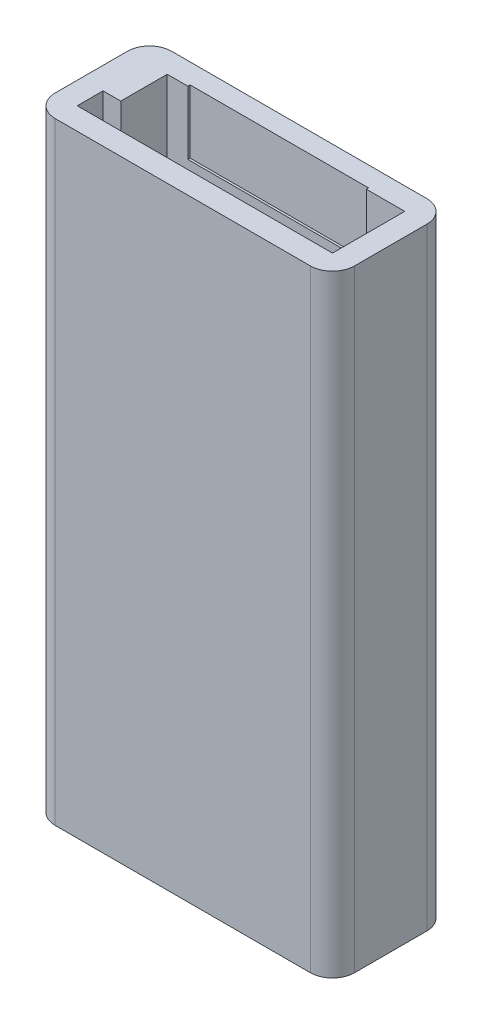
SolidWorks part; units mm, degrees
ref_plane "Front Plane" through (0, 0, 0) normal (0, 0, 1) x (1, 0, 0)
ref_plane "Top Plane" through (0, 0, 0) normal (0, 1, 0) x (1, 0, 0)
ref_plane "Right Plane" through (0, 0, 0) normal (1, 0, 0) x (0, 0, -1)
sketch "Sketch1" plane through (0, 0, 0) normal (0, 1, 0) x (1, 0, 0)
  line L0 (10.15, -3.95) -> (10.15, 3.95)
  line L1 (8.65, -2.45) -> (-8.65, -2.45)
  line L2 (8.65, -2.45) -> (8.65, 2.45)
  line L3 (8.65, 2.45) -> (-8.65, 2.45)
  line L4 (-8.65, -2.45) -> (-8.65, 2.45)
  line L5 (8.65, -2.45) -> (-8.65, 2.45) construction
  line L6 (8.65, 2.45) -> (-8.65, -2.45) construction
  line L7 (10.15, 3.95) -> (-10.15, 3.95)
  line L8 (-10.15, -3.95) -> (-10.15, 3.95)
  line L9 (10.15, -3.95) -> (-10.15, -3.95)
  point P0 (0, 0)
  dimension "D1" = 17.3
  dimension "D2" = 4.9
  dimension "D3" = 1.5
extrude "Boss-Extrude1" add sketch "Sketch1" along normal blind 41.5
sketch "Sketch2" plane through (0, 0, 0) normal (0, -1, 0) x (1, 0, 0)
  line L0 (-10.15, 3.95) -> (10.15, 3.95) construction
  line L1 (-10.15, -3.95) -> (-10.15, 3.95) construction
  line L2 (-10.15, 3.95) -> (10.15, 3.95)
  line L3 (-10.15, -3.95) -> (-10.15, 3.95)
  line L4 (10.15, -3.95) -> (-10.15, -3.95) construction
  line L5 (10.15, 3.95) -> (10.15, -3.95) construction
  line L6 (10.15, -3.95) -> (-10.15, -3.95)
  line L7 (10.15, 3.95) -> (10.15, -3.95)
extrude "Boss-Extrude2" add sketch "Sketch2" against normal blind 1.5
sketch "Sketch3" plane through (0, 1.5, 0) normal (0, 1, 0) x (1, 0, 0)
  line L0 (-8.65, -2.45) -> (8.65, -2.45) construction
  line L1 (-8.65, 2.45) -> (-7.45, 2.45)
  line L2 (-8.65, 2.45) -> (-8.65, -0.7)
  line L3 (-8.65, -0.7) -> (-7.45, -0.7)
  line L4 (-7.45, 2.45) -> (-7.45, -0.7)
  dimension "D1" = 1.2
  dimension "D2" = 1.75
extrude "Boss-Extrude3" add sketch "Sketch3" along normal up to surface (40 mm away) up to face at (0, 41.5, 0)
sketch "Sketch4" plane through (0, 1.5, 0) normal (0, 1, 0) x (1, 0, 0)
  line L0 (-8.65, -0.7) -> (-7.45, -0.7) construction
  line L1 (8.65, 2.45) -> (7.45, 2.45)
  line L2 (8.65, 2.45) -> (8.65, -0.7)
  line L3 (8.65, -0.7) -> (7.45, -0.7)
  line L4 (7.45, 2.45) -> (7.45, -0.7)
  line L5 (-7.45, -0.7) -> (-8.65, -0.7) construction
extrude "Boss-Extrude4" add sketch "Sketch4" along normal blind 17
sketch "Sketch5" plane through (0, 41.5, 0) normal (0, 1, 0) x (1, 0, 0)
  line L0 (7.45, 2.45) -> (-7.45, 2.45) construction
  line L1 (6.05, 2.3) -> (-6.05, 2.3)
  line L2 (6.05, 2.3) -> (6.05, 2.6)
  line L3 (6.05, 2.6) -> (-6.05, 2.6)
  line L4 (-6.05, 2.3) -> (-6.05, 2.6)
  line L5 (6.05, 2.3) -> (-6.05, 2.6) construction
  line L6 (6.05, 2.6) -> (-6.05, 2.3) construction
  line L7 (-8.65, -2.45) -> (8.65, -2.45) construction
  point P0 (0, 2.45)
  dimension "D1" = 12.1
  dimension "D2" = 5.05
extrude "Cut-Extrude1" cut sketch "Sketch5" against normal offset from surface (4.3 mm away) 35.7 up to face at (0, 1.5, 0.35)
fillet "Fillet1" radius 1.5 4 edges at (-10.15, 20.75, -3.95) (-10.15, 20.75, 3.95) (10.15, 20.75, 3.95) (10.15, 20.75, -3.95)
